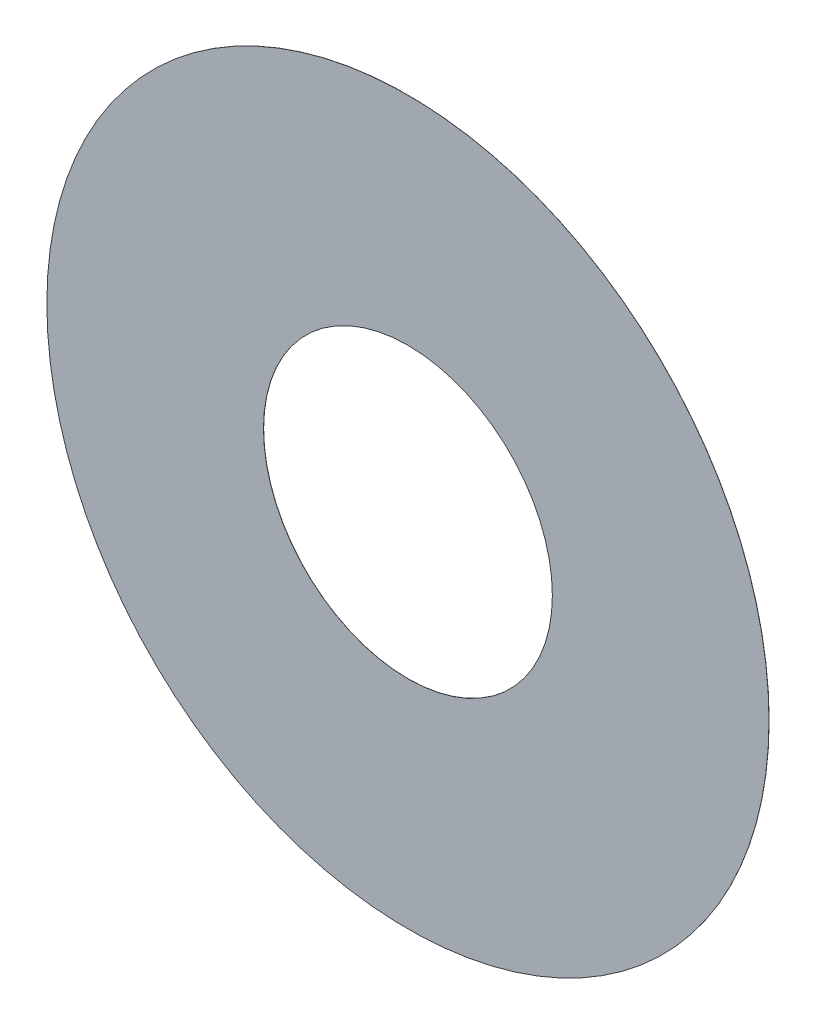
SolidWorks part; units mm, degrees
ref_plane "Płaszczyzna przednia" through (0, 0, 0) normal (0, 0, 1) x (1, 0, 0)
ref_plane "Płaszczyzna górna" through (0, 0, 0) normal (0, 1, 0) x (1, 0, 0)
ref_plane "Płaszczyzna prawa" through (0, 0, 0) normal (1, 0, 0) x (0, 0, -1)
sketch "Szkic1" plane through (0, 0, 0) normal (0, 0, 1) x (1, 0, 0)
  circle A0 centre (0, 0) radius 25
  circle A1 centre (0, 0) radius 10
  dimension "D1" = 50
  dimension "D2" = 20
extrude "Dodanie-wyciągnięcie1" add sketch "Szkic1" along normal blind 0.01
